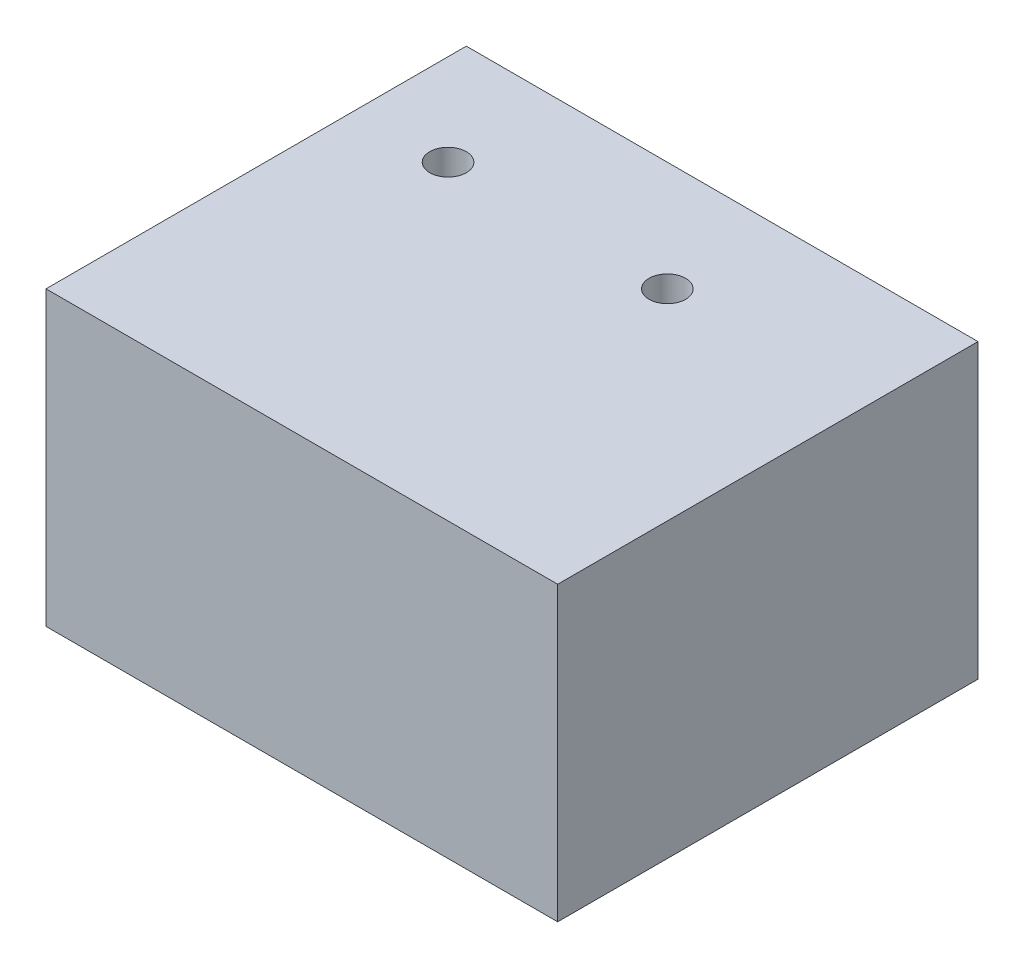
SolidWorks part; units mm, degrees
ref_plane "Front Plane" through (0, 0, 0) normal (0, 0, 1) x (1, 0, 0)
ref_plane "Top Plane" through (0, 0, 0) normal (0, 1, 0) x (1, 0, 0)
ref_plane "Right Plane" through (0, 0, 0) normal (1, 0, 0) x (0, 0, -1)
sketch "Sketch1" plane through (0, 0, 0) normal (0, 1, 0) x (1, 0, 0)
  line L1 (-46.0948, -23.9532) -> (93.9052, -23.9532)
  line L2 (-46.0948, -23.9532) -> (-46.0948, 91.0468)
  line L3 (-46.0948, 91.0468) -> (93.9052, 91.0468)
  line L4 (93.9052, -23.9532) -> (93.9052, 91.0468)
extrude "Boss-Extrude1" add sketch "Sketch1" along normal blind 80
ref_plane "Plane1" through (0, 0, -91.0468) normal (0, 0, -1) x (-1, 0, 0)
sketch "Sketch3" plane through (0, 0, -91.0468) normal (0, 0, -1) x (-1, 0, 0)
  line L0 (-93.9052, 80) -> (46.0948, 80) construction
  line L1 (-86.9052, 7) -> (39.0948, 7)
  line L2 (-86.9052, 7) -> (-86.9052, 73)
  line L3 (-86.9052, 73) -> (39.0948, 73)
  line L4 (39.0948, 7) -> (39.0948, 73)
  line L5 (-93.9052, 80) -> (-93.9052, 0) construction
  line L6 (-93.9052, 0) -> (46.0948, 0) construction
  line L7 (46.0948, 80) -> (46.0948, 0) construction
  dimension "D1" = 7
  dimension "D2" = 7
  dimension "D3" = 7
  dimension "D4" = 7
extrude "Cut-Extrude1" cut sketch "Sketch3" against normal blind 108
ref_plane "Plane2" through (0, 80, 0) normal (0, 1, 0) x (1, 0, 0)
sketch "Sketch4" plane through (0, 80, 0) normal (0, 1, 0) x (1, 0, 0)
  line L0 (93.9052, 91.0468) -> (-46.0948, 91.0468) construction
  line L1 (-46.0948, 91.0468) -> (-46.0948, -23.9532) construction
  point P0 (-21.0948, 61.0468)
  point P1 (38.9052, 61.0468)
  dimension "D1" = 30
  dimension "D2" = 25
  dimension "D3" = 60
  dimension "D4" = 30
hole_wizard "M10x1.0 Tapped Hole1" positions "Sketch6" profile "Sketch5" tap size "M10x1.0" standard "ANSI Metric"
sketch "Sketch6" plane through (0, 80, 0) normal (0, 1, 0) x (1, 0, 0)
  point P0 (-21.0948, 61.0468)
  point P3 (38.9052, 61.0468)
sketch "Sketch5" plane through (-21.0948, 80, -61.0468) normal (1, 0, 0) x (0, 0, 1)
  line L0 (0, 0) -> (0, 25.7039)
  line L1 (0, 25.7039) -> (4.5, 23)
  line L2 (4.5, 23) -> (4.5, 20)
  line L3 (4.5, 20) -> (5, 20)
  line L4 (5, 20) -> (5, 0)
  line L5 (5, 0) -> (0, 0)
  line L10 (0, 25.7039) -> (-4.5, 23) construction
  line L11 (0, -6.35) -> (0, 107.95) construction
  dimension "Tap Drill Dia." = 9
  dimension "Tap Drill Depth" = 23
  dimension "Thread Major Dia." = 10
  dimension "Thread Depth" = 20
  dimension "Drill Angle" = 118
ref_plane "Plane3" through (-46.0948, 0, 0) normal (-1, 0, 0) x (0, 0, 1)
sketch "Sketch7" plane through (-46.0948, 0, 0) normal (-1, 0, 0) x (0, 0, 1)
  line L0 (-91.0468, 80) -> (-91.0468, 0) construction
  line L1 (-91.0468, 80) -> (23.9532, 80) construction
  point P0 (-51.0468, 15)
  dimension "D1" = 40
  dimension "D2" = 65
hole_wizard "M10x1.0 Tapped Hole2" positions "Sketch9" profile "Sketch8" tap size "M10x1.0" standard "ANSI Metric"
sketch "Sketch9" plane through (-46.0948, 0, 0) normal (-1, 0, 0) x (0, 0, 1)
  point P0 (-51.0468, 15)
sketch "Sketch8" plane through (-46.0948, 15, -51.0468) normal (0, 1, 0) x (0, 0, 1)
  line L0 (0, 0) -> (0, 25.7039)
  line L1 (0, 25.7039) -> (4.5, 23)
  line L2 (4.5, 23) -> (4.5, 20)
  line L3 (4.5, 20) -> (5, 20)
  line L4 (5, 20) -> (5, 0)
  line L5 (5, 0) -> (0, 0)
  line L10 (0, 25.7039) -> (-4.5, 23) construction
  line L11 (0, -6.35) -> (0, 107.95) construction
  dimension "Tap Drill Dia." = 9
  dimension "Tap Drill Depth" = 23
  dimension "Thread Major Dia." = 10
  dimension "Thread Depth" = 20
  dimension "Drill Angle" = 118
